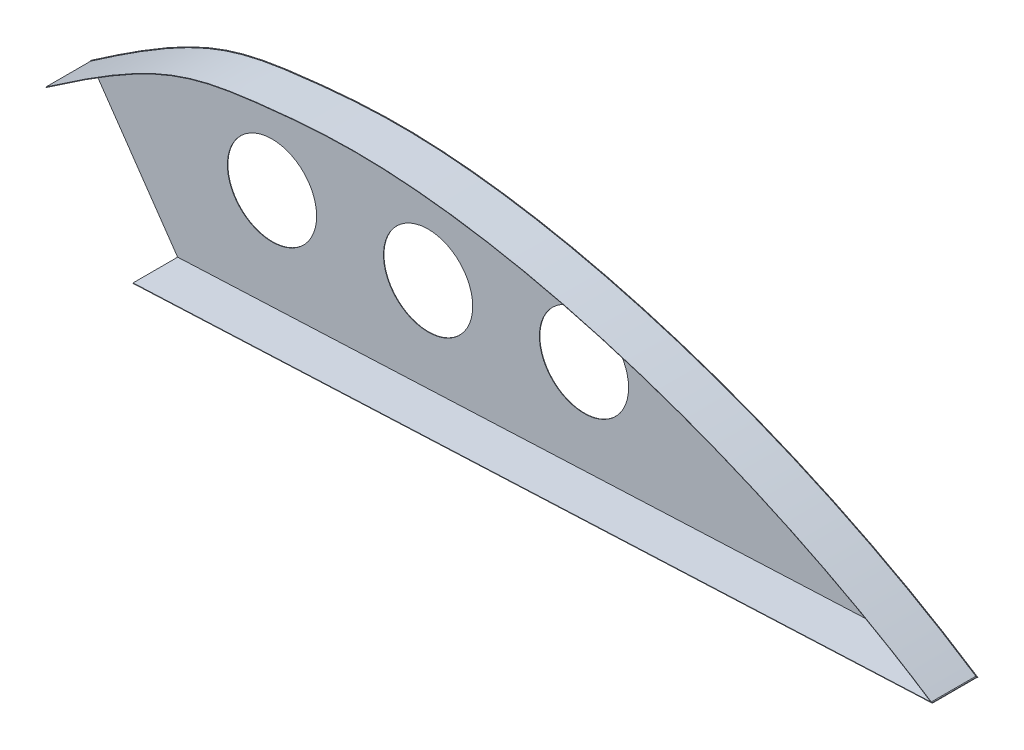
SolidWorks part; units mm, degrees
ref_plane "Front Plane" through (0, 0, 0) normal (0, 0, 1) x (1, 0, 0)
ref_plane "Top Plane" through (0, 0, 0) normal (0, 1, 0) x (1, 0, 0)
ref_plane "Right Plane" through (0, 0, 0) normal (1, 0, 0) x (0, 0, -1)
sketch "Sketch1" plane through (0, 0, 0) normal (0, 0, 1) x (1, 0, 0)
  line L0 (-169.0031, 11.7142) -> (-694.187, 895.1707) construction
  line L1 (-1743.608, 593.8305) -> (-1544.65, 573.4414) construction
  line L2 (-1743.608, 593.8305) -> (-1723.9756, 565.3542)
  line L3 (-1723.9756, 565.3542) -> (-1544.65, 573.4414)
  line L4 (-1702.8657, 588.9864) -> (-1667.8657, 588.9864) construction
  line L5 (-1667.8657, 588.9864) -> (-1632.9063, 590.6708) construction
  circle A0 centre (-1632.9063, 590.6708) radius 10
  circle A1 centre (-1667.8657, 588.9864) radius 10
  circle A2 centre (-1702.8657, 588.9864) radius 10
  spline S0 degree 3 poles (-1743.608, 593.8305) (-1719.5079, 610.5378) (-1709.3895, 613.3998) (-1646.2803, 619.2418) (-1585.7166, 600.4239) (-1544.65, 573.4414) knots 0 0 0 0 0.320555 0.420555 1 1 1 1
  dimension "D1" = 200
extrude "Boss-Extrude1" add sketch "Sketch1" along normal blind 0.1
sketch "Sketch2" plane through (0, 0, 0.1) normal (0, 0, 1) x (1, 0, 0)
  line L0 (-1723.9756, 565.3542) -> (-1544.7983, 573.4347)
  line L1 (-1544.8028, 573.5346) -> (-1544.7983, 573.4347)
  line L2 (-1723.9756, 565.3542) -> (-1724.0278, 565.4519)
  line L3 (-1544.8028, 573.5346) -> (-1724.0425, 565.4513)
  line L4 (-1743.608, 593.8305) -> (-1723.9756, 565.3542) construction
  line L5 (-1724.0425, 565.4513) -> (-1723.9756, 565.3542)
  line M5 (-1723.9756, 565.3542) -> (-1544.65, 573.4414)
extrude "Boss-Extrude2" add sketch "Sketch2" along normal blind 10 contours L1 L3 L2 M5
sketch "Sketch3" plane through (0, 0, 0.1) normal (0, 0, 1) x (1, 0, 0)
  line L0 (-1545.0231, 573.5666) -> (-1545.1827, 573.5516)
  line L1 (-1743.551, 593.7483) -> (-1743.494, 593.6661)
  spline S2 degree 1 poles (-1545.0779, 573.4829) (-1743.494, 593.6661) knots 0 0 1 1 construction
  spline S3 degree 3 poles (-4442.2408, 53.6236) (-858.6957, 47.7138) (-1418.8644, 592.6492) (-1664.0589, 615.5654) (-1668.4606, 615.8036) (-1674.8503, 615.8746) (-1676.9461, 615.8489) (-1681.0516, 615.7101) (-1685.0673, 615.4882) (-1688.837, 615.1571) (-1692.4504, 614.8003) (-1694.177, 614.6103) (-1699.0857, 614.0353) (-1702.0191, 613.6295) (-1710.3785, 612.0277) (-1715.3642, 610.448) (-1786.0484, 575.4737) (-1964.4305, 381.8355) (-4240.155, -1068.4995) knots -2.832341 -2.832341 -2.832341 -2.832341 0.5 0.5 0.5625 0.5625 0.59375 0.59375 0.625 0.65625 0.65625 0.6875 0.6875 0.75 0.75 0.875 0.875 2.236394 2.236394 2.236394 2.236394 only from (-1544.7049, 573.3579) to (-1743.551, 593.7483)
  spline S5 degree 3 poles (-1545.0231, 573.5666) (-1580.3856, 596.7218) (-1623.5401, 611.7785) (-1664.0589, 615.5654) (-1668.4606, 615.8036) (-1674.8503, 615.8746) (-1676.9461, 615.8489) (-1681.0516, 615.7101) (-1685.0673, 615.4882) (-1688.837, 615.1571) (-1692.4504, 614.8003) (-1694.177, 614.6103) (-1699.0857, 614.0353) (-1702.0191, 613.6295) (-1710.3785, 612.0277) (-1715.3642, 610.448) (-1727.2528, 604.5656) (-1734.1551, 600.262) (-1743.551, 593.7483) knots 0.001496 0.001496 0.001496 0.001496 0.5 0.5 0.5625 0.5625 0.59375 0.59375 0.625 0.65625 0.65625 0.6875 0.6875 0.75 0.75 0.875 0.875 1 1 1 1
  spline S6 degree 3 poles (-1545.0779, 573.4829) (-1547.2966, 574.9357) (-1551.7738, 577.764) (-1560.9656, 583.1745) (-1572.7958, 589.4305) (-1587.3762, 596.0941) (-1607.0889, 603.7942) (-1626.8603, 609.6331) (-1645.984, 613.4433) (-1659.8307, 615.2399) (-1672.9898, 615.9512) (-1683.2828, 615.5498) (-1690.8034, 614.8812) (-1697.6808, 614.1265) (-1704.9809, 613.1171) (-1711.56, 611.461) (-1716.9626, 609.4371) (-1721.2307, 607.489) (-1725.8593, 605.0309) (-1730.1358, 602.4915) (-1733.8809, 600.1254) (-1736.8678, 598.1747) (-1739.5261, 596.3902) (-1741.75, 594.8714) (-1742.9182, 594.0653) (-1743.494, 593.6661) knots 0.001496 0.001496 0.001496 0.001496 0.0327 0.063903 0.126309 0.188716 0.251122 0.375935 0.438342 0.500748 0.563155 0.625561 0.656764 0.687968 0.750374 0.812781 0.843984 0.875187 0.90639 0.937594 0.953195 0.968797 0.984398 0.992199 1 1 1 1 only from (-1545.1827, 573.5516) to (-1743.494, 593.6661)
  dimension "D1" = 0.1
  dimension "D3" = 0.1
extrude "Boss-Extrude5" add sketch "Sketch3" along normal blind 10
